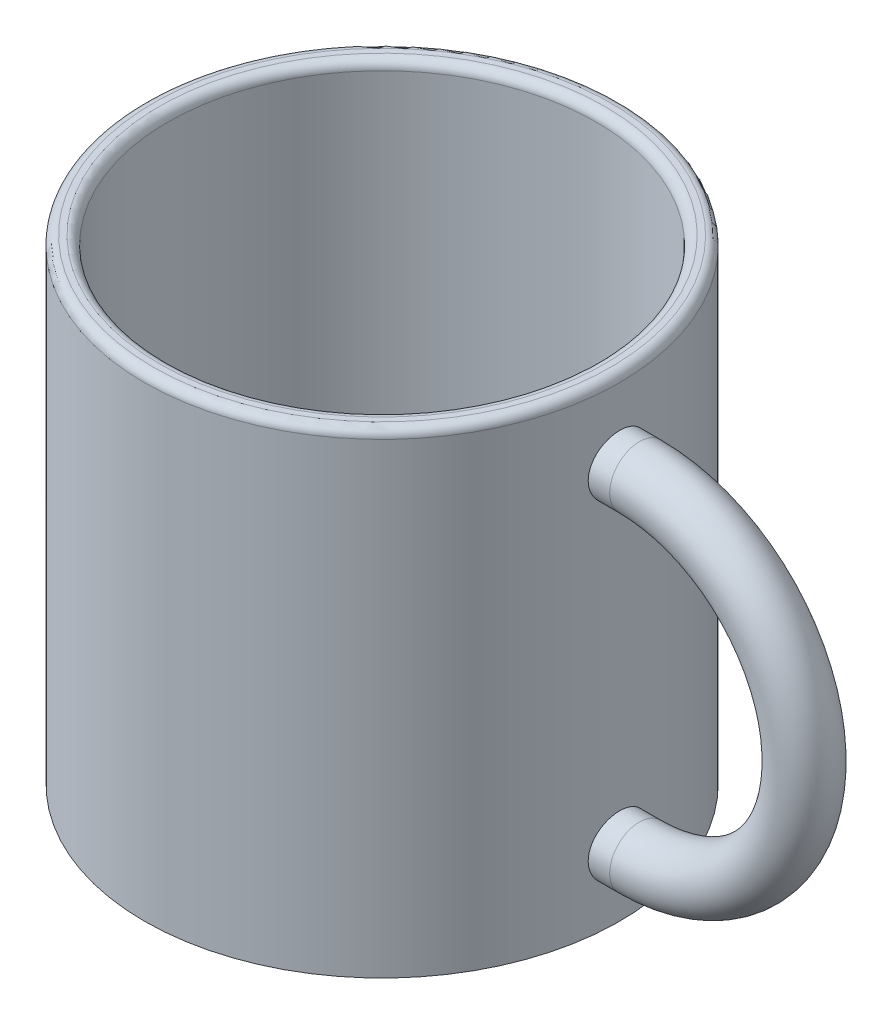
SolidWorks part; units mm, degrees
ref_plane "Front" through (0, 0, 0) normal (0, 0, 1) x (1, 0, 0)
ref_plane "Top" through (0, 0, 0) normal (0, 1, 0) x (1, 0, 0)
ref_plane "Right" through (0, 0, 0) normal (1, 0, 0) x (0, 0, -1)
sketch "Sketch1" plane through (0, 0, 0) normal (0, 1, 0) x (1, 0, 0)
  circle A0 centre (0, 0) radius 20
  dimension "D1" = 40
extrude "Extrude1" add sketch "Sketch1" along normal blind 40
sketch "Sketch2" plane through (0, 0, 0) normal (1, 0, 0) x (0, 0, -1)
  line L0 (0, 40) -> (0, 0) construction
  circle A0 centre (0, 33.273) radius 2.5
  dimension "D1" = 5
sketch "Sketch3" plane through (0, 0, 0) normal (0, 0, 1) x (1, 0, 0)
  line L0 (0, 30.773) -> (21.65, 30.773)
  line L1 (0, 30.773) -> (0, 35.773) construction
  line L2 (21.65, 8.053) -> (0, 8.053)
  line L3 (0, 40) -> (0, 0) construction
  arc A0 (21.65, 30.773) -> (21.65, 8.053) centre (21.65, 19.413) cw
  dimension "D2" = 11.36
  dimension "D1" = 21.65
sweep "Sweep1" add profiles "Sketch2" path "Sketch3"
sketch "Sketch4" plane through (0, 40, 0) normal (0, 1, 0) x (-1, 0, 0)
  circle A2 centre (0, 0) radius 18
  circle A3 centre (0, 0) radius 18
  dimension "D1" = 2
extrude "Cut-Extrude1" cut sketch "Sketch4" against normal offset from surface (38 mm away) 2 up to face at (0, 0, 20)
fillet "Fillet1" radius 0.75 2 edges at (0, 40, 20) (0, 40, 18)
fillet "Fillet2" radius 0.75 1 edges at (0, 2, 18)
scale "Scale1" scale about centroid uniform scaling yes scale factor 1
scale "Scale2" scale about centroid uniform scaling yes scale factor 1.8
